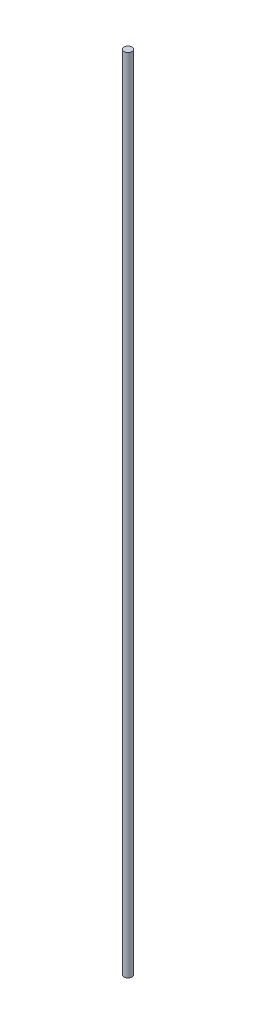
SolidWorks part; units mm, degrees
ref_plane "前视基准面" through (0, 0, 0) normal (0, 0, 1) x (1, 0, 0)
ref_plane "上视基准面" through (0, 0, 0) normal (0, 1, 0) x (1, 0, 0)
ref_plane "右视基准面" through (0, 0, 0) normal (1, 0, 0) x (0, 0, -1)
sketch "草图1" plane through (0, 0, 0) normal (0, 1, 0) x (1, 0, 0)
  circle A0 centre (0, 0) radius 1
extrude "凸台-拉伸1" add sketch "草图1" along normal blind 200
sketch "草图2" plane through (0, 200, 0) normal (0, 1, 0) x (1, 0, 0)
  point P0 (0, 0)
sketch "草图3" plane through (0, 0, 0) normal (0, -1, 0) x (1, 0, 0)
  point P0 (0, 0)
sketch "草图4" plane through (0, 0, 0) normal (1, 0, 0) x (0, 0, -1)
  line L0 (0, 200) -> (0, 0)
  line L1 (1, 200) -> (-1, 200) construction
